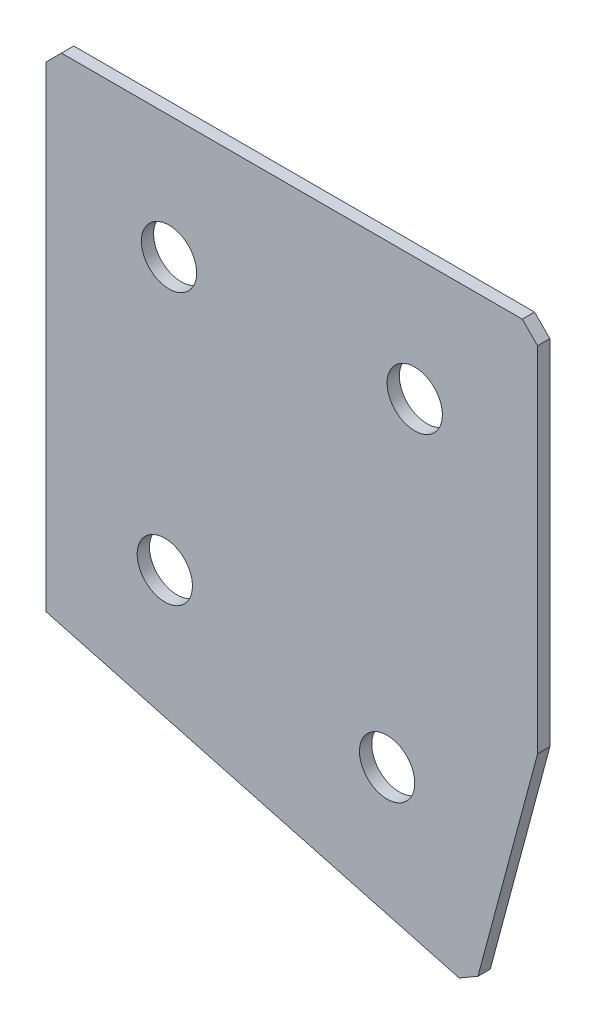
SolidWorks part; units mm, degrees
material "Простая углеродистая сталь"
ref_plane "Спереди" through (0, 0, 0) normal (0, 0, 1) x (1, 0, 0)
ref_plane "Сверху" through (0, 0, 0) normal (0, 1, 0) x (1, 0, 0)
ref_plane "Справа" through (0, 0, 0) normal (1, 0, 0) x (0, 0, -1)
sketch "Эскиз3" plane through (0, 0, 0) normal (0, 0, -1) x (1, 0, 0)
  line L0 (0, 0) -> (80, 0)
  line L1 (80, 0) -> (80, 60.0249)
  line L2 (0, 0) -> (0, 80)
  line L3 (0, 80) -> (69.6472, 98.6619)
  line L4 (69.6472, 98.6619) -> (80, 60.0249)
  dimension "D1" = 80
  dimension "D2" = 80
  dimension "D3" = 40
  dimension "D4" = 15
  dimension "D5" = 60.0249
extrude "Бобышка-Вытянуть1" add sketch "Эскиз3" along normal blind 2
hole_wizard "Отверстие с зазором M81" positions "Эскиз4" profile "Эскиз5" hole size "M8" standard "DIN" end condition through all
sketch "Эскиз4" plane through (0, 0, -2) normal (0, 0, -1) x (1, 0, 0)
  line L0 (19.3185, 64.4709) -> (55.5051, 74.167) construction
  line L2 (69.6472, 98.6619) -> (0, 80) construction
  line L3 (20, 20) -> (60, 20) construction
  line L5 (0, 0) -> (80, 0) construction
  line L6 (0, 80) -> (0, 0) construction
  line L7 (80, 0) -> (80, 60.0249) construction
  line L8 (80, 60.0249) -> (69.6472, 98.6619) construction
  line L9 (19.3185, 64.4709) -> (0, 59.2945) construction
  point P0 (20, 20)
  point P2 (60, 20)
  point P4 (19.3185, 64.4709)
  point P6 (55.5051, 74.167)
  dimension "D1" = 20
  dimension "D2" = 20
  dimension "D3" = 20
  dimension "D4" = 20
  dimension "D5" = 20
  dimension "D6" = 20
  dimension "D7" = 37.4631
  dimension "D8" = 40
sketch "Эскиз5" plane through (20, -20, -2) normal (1, 0, 0) x (0, 1, 0)
  line L0 (0, 0) -> (0, 2)
  line L1 (0, 2) -> (4.5, 2)
  line L2 (4.5, 2) -> (4.5, 0)
  line L5 (4.5, 0) -> (0, 0)
  line L11 (0, -6.35) -> (0, 107.95) construction
  dimension "Диаметр сквозного отверстия" = 9
  dimension "Глубина сквозного отверстия" = 2
chamfer "Фаска1" distance 2.5 distance2 2.5 3 edges at (69.6472, -98.6619, -1) (80, 0, -1) (0, 0, -1)
